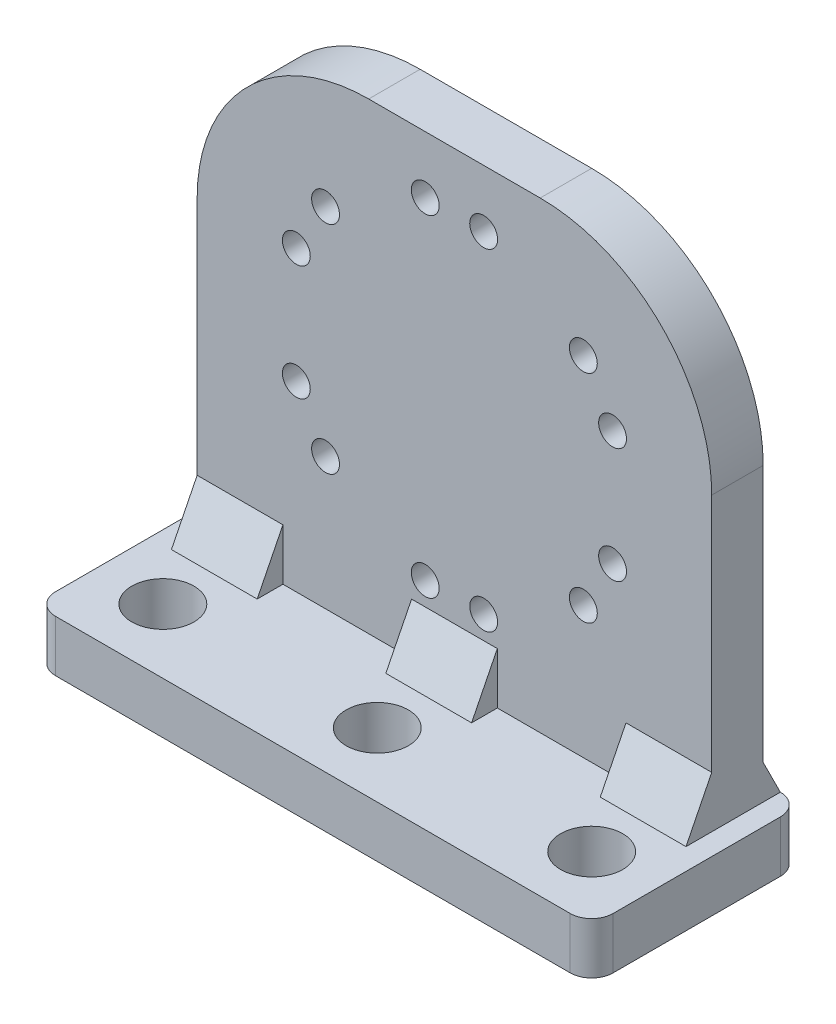
SolidWorks part; units mm, degrees
ref_plane "정면" through (0, 0, 0) normal (0, 0, 1) x (1, 0, 0)
ref_plane "윗면" through (0, 0, 0) normal (0, 1, 0) x (1, 0, 0)
ref_plane "우측면" through (0, 0, 0) normal (1, 0, 0) x (0, 0, -1)
sketch "Sketch1" plane through (0, 0, 0) normal (0, 0, 1) x (1, 0, 0)
  line L0 (30, 0) -> (0, 0) construction
  line L1 (-30, 30) -> (30, 30)
  line L2 (-30, 30) -> (-30, -30)
  line L3 (-30, -30) -> (30, -30)
  line L4 (30, 30) -> (30, -30)
  dimension "D1" = 60
  dimension "D2" = 60
  dimension "D3" = 30
extrude "Boss-Extrude1" add sketch "Sketch1" along normal blind 6
sketch "Sketch2" plane through (0, 0, 6) normal (0, 0, 1) x (1, 0, 0)
  line L0 (30, -30) -> (30, 30) construction
  line L1 (30, -24) -> (20, -24)
  line L2 (30, -24) -> (30, -30)
  line L3 (30, -30) -> (20, -30)
  line L4 (20, -24) -> (20, -30)
  line L5 (-30, -30) -> (30, -30) construction
  line L6 (0, 0) -> (0, -30) construction
  line L7 (0, -30) -> (25, -30) construction
  dimension "D1" = 25
  dimension "D2" = 10
  dimension "D3" = 6
extrude "Boss-Extrude2" add sketch "Sketch2" along normal blind 14 contours L1 L4 L3 L2
sketch "Sketch3" plane through (30, 0, 0) normal (1, 0, 0) x (0, 0, -1)
  line L0 (-6, -18) -> (-9, -24)
  line L1 (-6, -24) -> (-6, 30) construction
  line L2 (-20, -24) -> (-6, -24) construction
  line L3 (-9, -24) -> (-6, -24)
  line L4 (-6, -24) -> (-6, -18)
  line L5 (0, -20) -> (2, -24)
  line L6 (0, -30) -> (0, 30) construction
  line L7 (2, -24) -> (0, -24)
  line L8 (0, -24) -> (0, -20)
  point P13 (3, -22.2476)
  dimension "D1" = 6
  dimension "D2" = 3
  dimension "D3" = 2
  dimension "D4" = 4
extrude "Boss-Extrude3" add sketch "Sketch3" against normal up to surface (10 mm away) up to face at (20, -27, 13)
sketch "Sketch4" plane through (0, -24, 0) normal (0, 1, 0) x (1, 0, 0)
  line L0 (25, -20) -> (25, 0) construction
  line L1 (30, -20) -> (20, -20) construction
  line L2 (30, 0) -> (-30, 0) construction
  circle A0 centre (25, -15) radius 3.625
  dimension "D1" = 7.25
  dimension "D2" = 5
extrude "Cut-Extrude1" cut sketch "Sketch4" against normal blind 15
pattern_linear "LPattern2" count 3 spacing 25 along (-1, 0, 0) of "Cut-Extrude1", "Boss-Extrude2", "Boss-Extrude3"
sketch "Sketch5" plane through (0, 0, 0) normal (0, 0, -1) x (-1, 0, 0)
  line L0 (0, 4) -> (0, 23.62) construction
  line L1 (0, 4) -> (3.407, 23.3219) construction
  line L2 (0, 4) -> (-3.407, 23.3219) construction
  line L3 (0, 4) -> (0, -30) construction
  line L4 (-5, -30) -> (5, -30) construction
  circle A0 centre (3.407, 23.3219) radius 1.625
  circle A1 centre (-3.407, 23.3219) radius 1.625
  dimension "D3" = 3.25
  dimension "D5" = 3.25
  dimension "D1" = 19.62
  dimension "D2" = 10
  dimension "D4" = 10
  dimension "D6" = 34
extrude "Cut-Extrude2" cut sketch "Sketch5" against normal blind 15
ref_plane "Plane1" through (0, 4, 0) normal (0, -1, 0) x (-1, 0, 0)
sketch "Sketch8" plane through (0, 4, 0) normal (0, -1, 0) x (-1, 0, 0)
  line L0 (0, 0) -> (0, -7.3713) construction
pattern_circular "CirPattern2" count 6 every 60 about axis through (0, 4, 0) along (0, 0, 1) of "Cut-Extrude2"
fillet "Fillet1" radius 20 2 edges at (-30, 30, 3) (30, 30, 3)
sketch "스케치3" plane through (0, -30, 0) normal (0, -1, 0) x (1, 0, 0)
  line L1 (-32.5, 22.5) -> (32.5, 22.5)
  line L2 (-32.5, 22.5) -> (-32.5, -17.5)
  line L3 (-32.5, -17.5) -> (32.5, -17.5)
  line L4 (32.5, 22.5) -> (32.5, -17.5)
  circle A0 centre (-25, 15) radius 3.625
  circle A1 centre (0, 15) radius 3.625
  circle A2 centre (25, 15) radius 3.625
  circle A3 centre (25, 15) radius 3.625 construction
  circle A4 centre (0, 15) radius 3.625 construction
  circle A5 centre (-25, 15) radius 3.625 construction
  circle A6 centre (-25, -10) radius 3.625
  circle A7 centre (0, -10) radius 3.625
  circle A8 centre (25, -10) radius 3.625
  point P22 (0, 0)
  point P23 (0, 0)
  point P24 (0, 0)
  point P25 (0, 0)
  point P26 (0, 0)
  dimension "D1" = 25
  dimension "D2" = 7.5
  dimension "D3" = 7.5
  dimension "D4" = 7.5
  dimension "D5" = 7.5
extrude "보스-돌출1" add sketch "스케치3" against normal up to surface (6 mm away) up to face at (-25, -24, 18.625)
sketch "스케치6" plane through (32.5, 0, 0) normal (1, 0, 0) x (0, 0, -1)
  line L0 (17.5, -30) -> (-22.5, -30) construction
  line L1 (17.5, -24) -> (2, -24)
  line L2 (17.5, -24) -> (17.5, -30)
  line L3 (17.5, -30) -> (2, -30)
  line L4 (2, -24) -> (2, -30)
  point P7 (0, 0)
extrude "컷-돌출2" cut sketch "스케치6" against normal up to surface (65 mm away) up to face at (-32.5, -27, 2.5)
fillet "필렛2" radius 2.5 4 edges at (-32.5, -27, 22.5) (-32.5, -27, -2) (32.5, -27, 22.5) (32.5, -27, -2)
sketch "스케치7" plane through (5, 0, 0) normal (1, 0, 0) x (0, 0, -1)
  line L1 (0, -20) -> (2, -20)
  line L2 (0, -20) -> (0, -24)
  line L3 (0, -24) -> (2, -24)
  line L4 (2, -20) -> (2, -24)
  point P6 (2.958, -23.9161)
  point P7 (3.5535, -24.1515)
extrude "컷-돌출3" cut sketch "스케치7" against normal up to surface (10 mm away) up to face at (-5, -22.6667, -0.6667)
